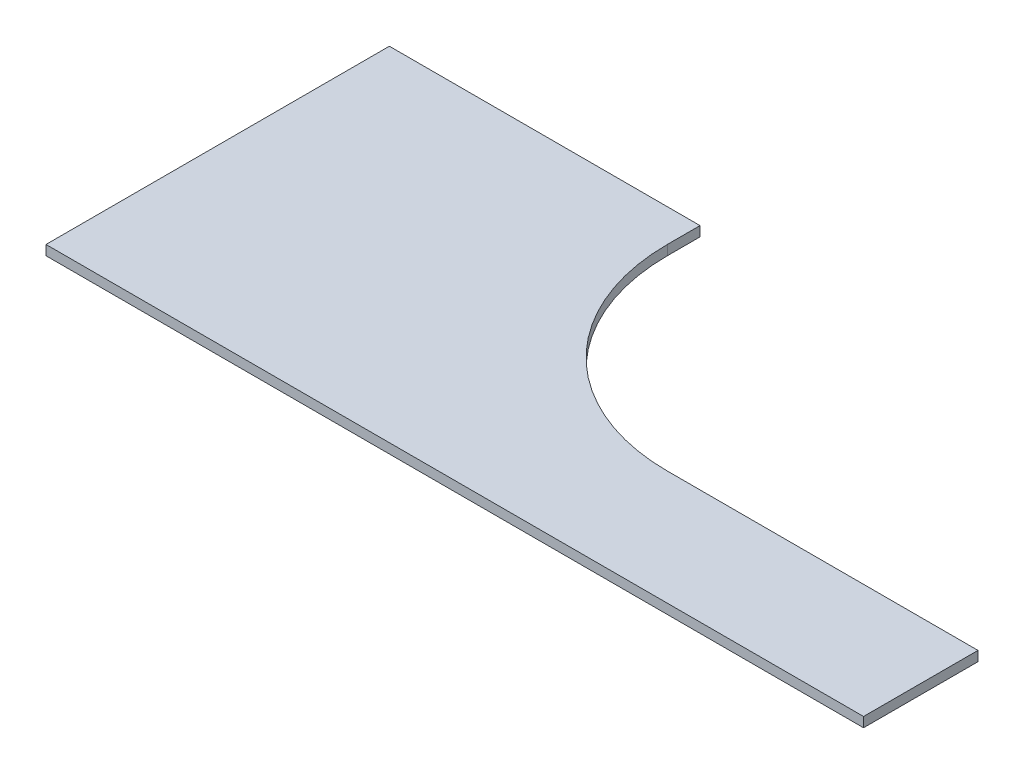
SolidWorks part; units mm, degrees
ref_plane "Front Plane" through (0, 0, 0) normal (0, 0, 1) x (1, 0, 0)
ref_plane "Top Plane" through (0, 0, 0) normal (0, 1, 0) x (1, 0, 0)
ref_plane "Right Plane" through (0, 0, 0) normal (1, 0, 0) x (0, 0, -1)
sketch "Sketch1" plane through (0, 0, 0) normal (0, 1, 0) x (1, 0, 0)
  line L0 (-10, 70) -> (-10, 90)
  line L1 (-10, 90) -> (-200, 90)
  line L2 (-200, 90) -> (-200, -120)
  line L3 (-200, -120) -> (300, -120)
  line L4 (300, -120) -> (300, -50)
  line L5 (300, -50) -> (110, -50)
  arc A0 (110, -50) -> (-10, 70) centre (110, 70) cw
extrude "Boss-Extrude1" add sketch "Sketch1" against normal blind 6
scale "Scale1" scale about centroid uniform scaling yes scale factor 0.75
